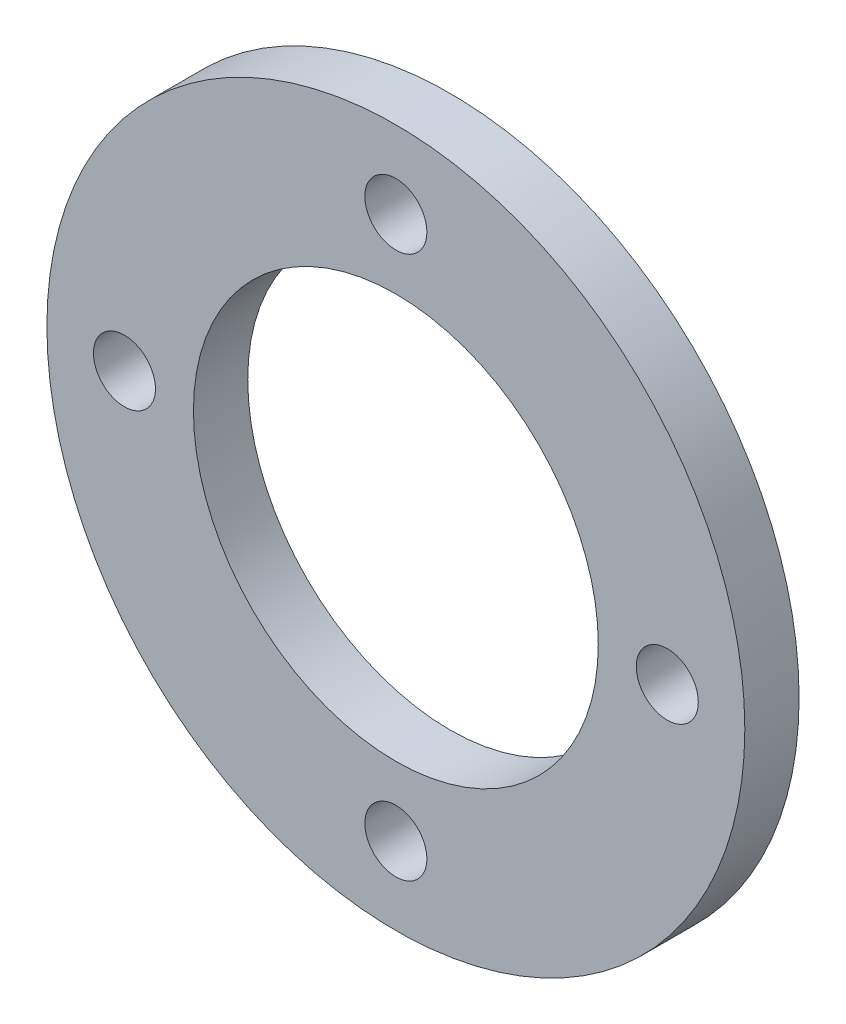
SolidWorks part; units mm, degrees
ref_plane "Alzado" through (0, 0, 0) normal (0, 0, 1) x (1, 0, 0)
ref_plane "Planta" through (0, 0, 0) normal (0, 1, 0) x (1, 0, 0)
ref_plane "Vista lateral" through (0, 0, 0) normal (1, 0, 0) x (0, 0, -1)
sketch "Croquis1" plane through (0, 0, 0) normal (0, 0, 1) x (1, 0, 0)
  circle A0 centre (0, 0) radius 45
  dimension "D1" = 90
extrude "Saliente-Extruir1" add sketch "Croquis1" along normal blind 7
sketch "Croquis2" plane through (0, 0, 7) normal (0, 0, 1) x (1, 0, 0)
  circle A0 centre (0, 0) radius 26.1
  dimension "D1" = 52.2
extrude "Cortar-Extruir1" cut sketch "Croquis2" against normal through all
sketch "Croquis3" plane through (0, 0, 7) normal (0, 0, 1) x (1, 0, 0)
  line L0 (45, 0) -> (-45, 0) construction
  line L1 (0, 45) -> (0, -45) construction
  circle A0 centre (0, 0) radius 45 construction
  circle A2 centre (0, 35) radius 4
  circle A3 centre (35, 0) radius 4
  circle A4 centre (0, -35) radius 4
  circle A5 centre (-35, 0) radius 4
  circle A6 centre (0, 0) radius 35 construction
  point P20 (0, 0)
  dimension "D1" = 70
  dimension "D3" = 8
  dimension "D2" = 4
extrude "Cortar-Extruir2" cut sketch "Croquis3" against normal through all
